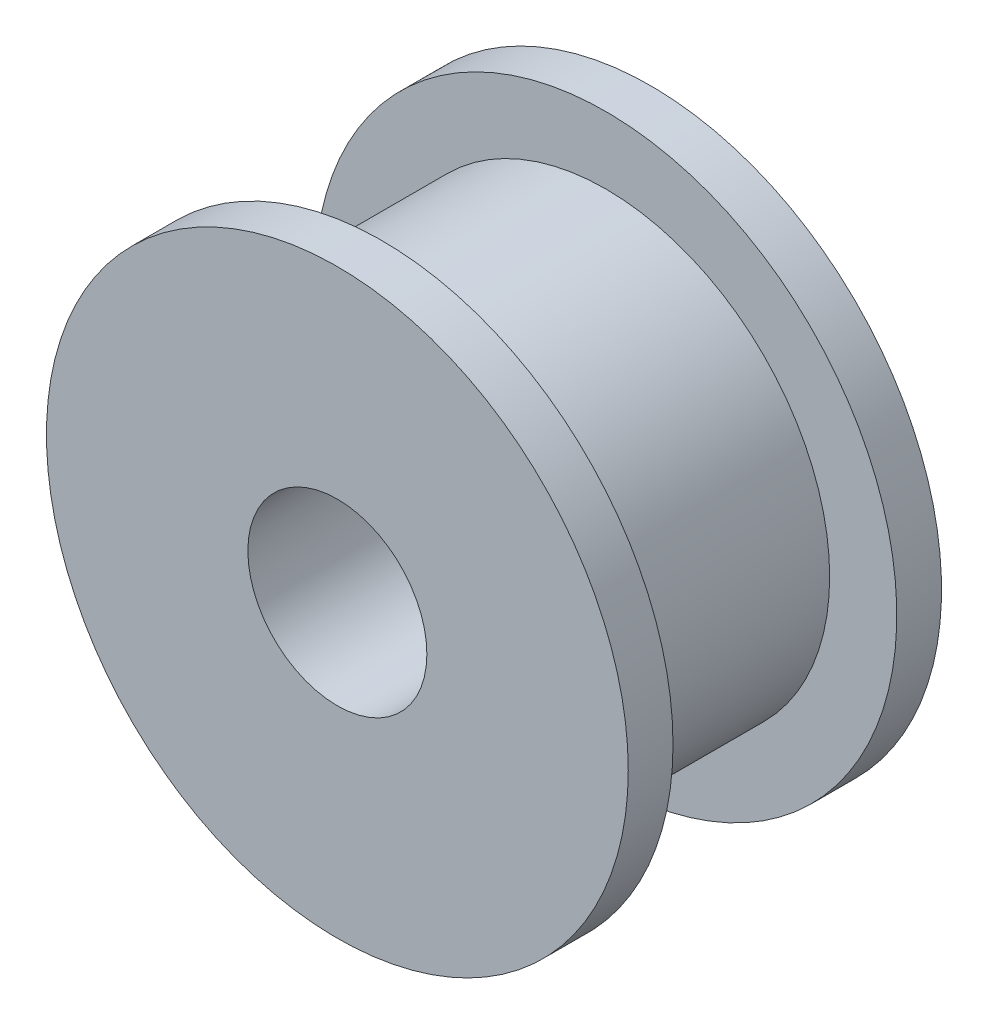
SolidWorks part; units mm, degrees
ref_plane "정면" through (0, 0, 0) normal (0, 0, 1) x (1, 0, 0)
ref_plane "윗면" through (0, 0, 0) normal (0, 1, 0) x (1, 0, 0)
ref_plane "우측면" through (0, 0, 0) normal (1, 0, 0) x (0, 0, -1)
sketch "스케치1" plane through (0, 0, 0) normal (0, 0, 1) x (1, 0, 0)
  circle A0 centre (0, 0) radius 5
  circle A1 centre (0, 0) radius 2
  dimension "D1" = 10
  dimension "D2" = 4
extrude "보스-돌출1" add sketch "스케치1" along normal mid plane 5
sketch "스케치2" plane through (0, 0, -2.5) normal (0, 0, -1) x (-1, 0, 0)
  circle A0 centre (0, 0) radius 2
  circle A1 centre (0, 0) radius 6.5
  circle A2 centre (0, 0) radius 2 construction
  dimension "D1" = 13
extrude "보스-돌출2" add sketch "스케치2" along normal blind 1
sketch "스케치3" plane through (0, 0, 2.5) normal (0, 0, 1) x (1, 0, 0)
  circle A0 centre (0, 0) radius 2
  circle A1 centre (0, 0) radius 6.5
  circle A2 centre (0, 0) radius 2 construction
  circle A3 centre (0, 0) radius 6.5 construction
extrude "보스-돌출3" add sketch "스케치3" along normal blind 1
